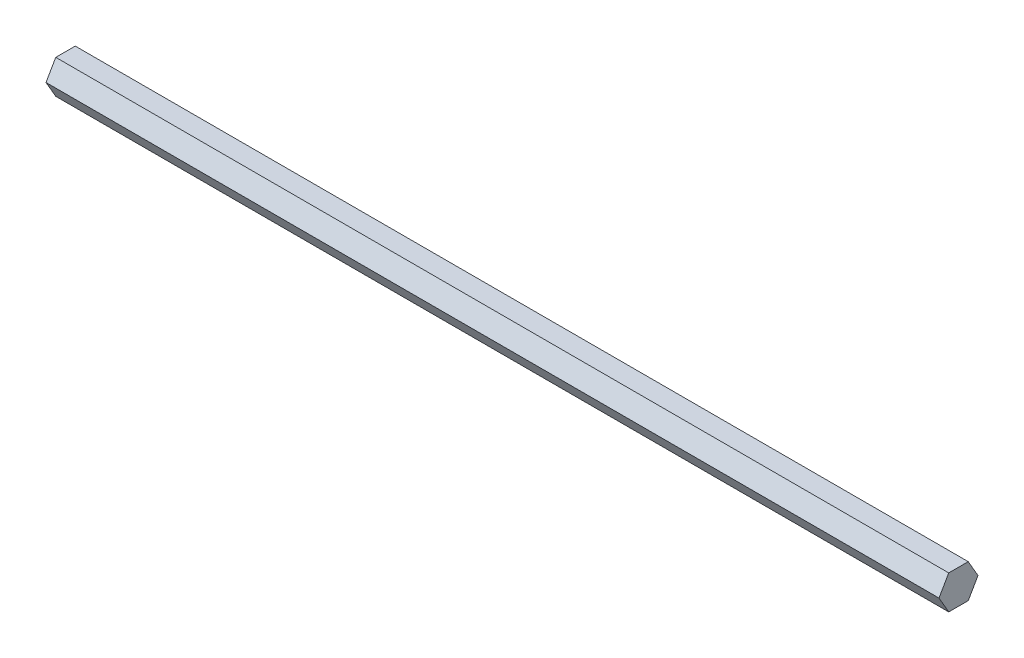
SolidWorks part; units mm, degrees
ref_plane "Спереди" through (0, 0, 0) normal (0, 0, 1) x (1, 0, 0)
ref_plane "Сверху" through (0, 0, 0) normal (0, 1, 0) x (1, 0, 0)
ref_plane "Справа" through (0, 0, 0) normal (1, 0, 0) x (0, 0, -1)
sketch "Эскиз1" plane through (0, 0, 0) normal (1, 0, 0) x (0, 0, -1)
  line L1 (8.0829, 0) -> (4.0415, 7)
  line L2 (4.0415, 7) -> (-4.0415, 7)
  line L3 (-4.0415, 7) -> (-8.0829, 0)
  line L4 (-8.0829, 0) -> (-4.0415, -7)
  line L5 (-4.0415, -7) -> (4.0415, -7)
  line L6 (4.0415, -7) -> (8.0829, 0)
  circle A0 centre (0, 0) radius 7 construction
extrude "Бобышка-Вытянуть1" add sketch "Эскиз1" along normal blind 370
